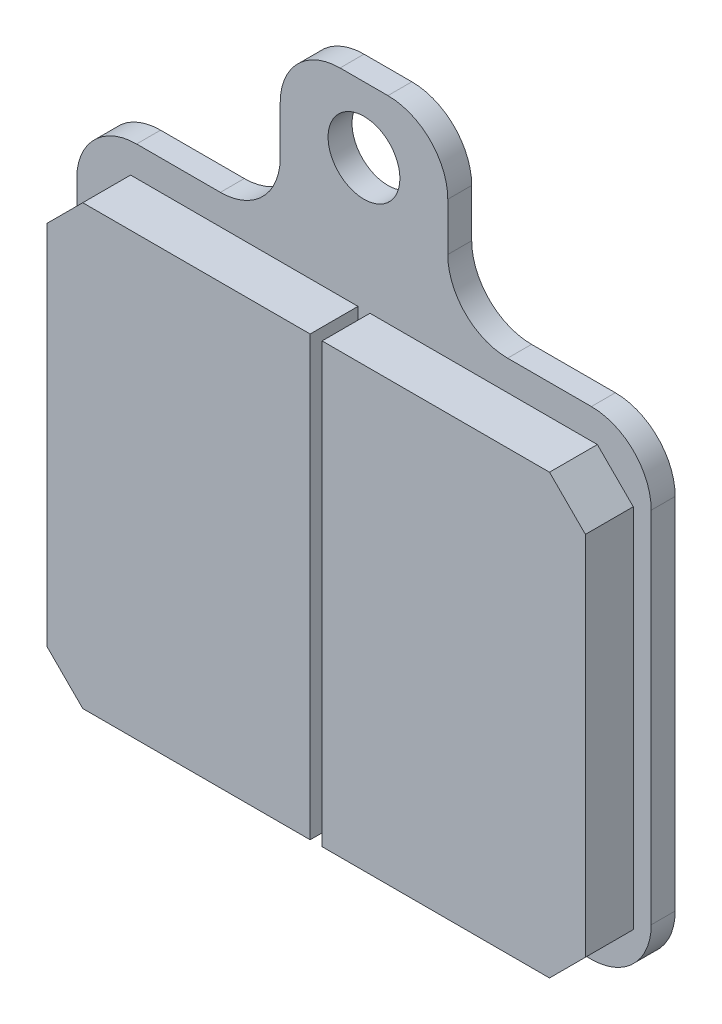
SolidWorks part; units mm, degrees
material "Ceramic Porcelain"
ref_plane "Front Plane" through (0, 0, 0) normal (0, 0, 1) x (1, 0, 0)
ref_plane "Top Plane" through (0, 0, 0) normal (0, 1, 0) x (1, 0, 0)
ref_plane "Right Plane" through (0, 0, 0) normal (1, 0, 0) x (0, 0, -1)
sketch "Sketch1" plane through (0, 0, 0) normal (0, 0, 1) x (1, 0, 0)
  line L1 (24, -20) -> (-24, -20)
  line L2 (24, -20) -> (24, 20)
  line L3 (24, 20) -> (7, 20)
  line L4 (-24, -20) -> (-24, 20)
  line L5 (24, -20) -> (-24, 20) construction
  line L6 (24, 20) -> (-24, -20) construction
  line L7 (-7, 20) -> (-24, 20)
  line L9 (7, 20) -> (7, 29)
  line L10 (2, 34) -> (-2, 34)
  line L11 (-7, 20) -> (-7, 29)
  circle A0 centre (0, 28.5) radius 3
  arc A1 (7, 29) -> (2, 34) centre (2, 29) ccw
  arc A2 (-2, 34) -> (-7, 29) centre (-2, 29) ccw
  point P0 (0, 0)
  point P9 (0, 24.25)
  dimension "D5" = 5
  dimension "D1" = 48
  dimension "D2" = 40
extrude "Boss-Extrude1" add sketch "Sketch1" along normal blind 2
sketch "Sketch2" plane through (0, 0, 2) normal (0, 0, 1) x (1, 0, 0)
  line L0 (-22.5, -17.5) -> (-22.5, -19.1004)
  line L1 (-0.5, -17.5) -> (-0.5, -19.1004)
  line L2 (22.5, -17.5) -> (22.5, 17.5)
  line L3 (22.5, 17.5) -> (0.5, 17.5)
  line L4 (-22.5, -17.5) -> (-22.5, 17.5)
  line L5 (-0.5, 17.5) -> (-22.5, 17.5)
  line L6 (0.5, -17.5) -> (0.5, 17.5)
  line L7 (-22.5, -19.1004) -> (-0.5, -19.1004)
  line L8 (22.5, -19.1004) -> (22.5, -17.5)
  line L9 (0.5, -19.1004) -> (22.5, -19.1004)
  line L10 (-0.5, -17.5) -> (-0.5, 17.5)
  line L14 (0.5, -17.5) -> (0.5, -19.1004)
  point P0 (0, 0)
  point P6 (0, 0)
  point P13 (0, 0)
  dimension "D1" = 45
  dimension "D2" = 35
  dimension "D3" = 1
extrude "Boss-Extrude2" add sketch "Sketch2" along normal blind 4
chamfer "Chamfer1" distance 3 angle 45 4 edges at (22.5, -19.1004, 4) (22.5, 17.5, 4) (-22.5, -19.1004, 4) (-22.5, 17.5, 4)
fillet "Fillet1" radius 5 6 edges at (7, 20, 1) (-7, 20, 1) (-24, -20, 1) (24, -20, 1) (24, 20, 1) (-24, 20, 1)
